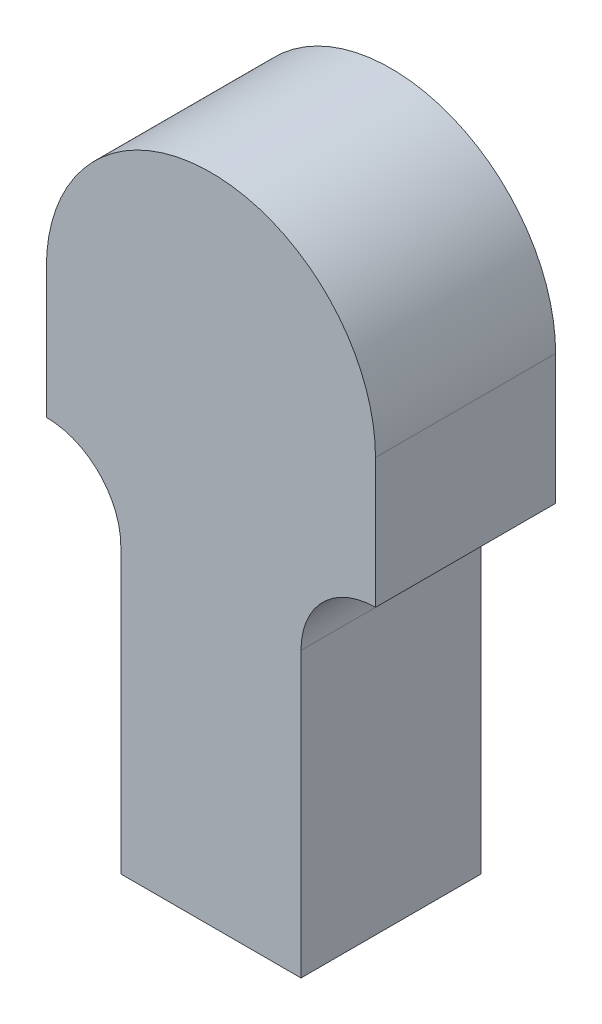
SolidWorks part; units mm, degrees
material "Stainless Steel (ferritic)"
ref_plane "Front Plane" through (0, 0, 0) normal (0, 0, 1) x (1, 0, 0)
ref_plane "Top Plane" through (0, 0, 0) normal (0, 1, 0) x (1, 0, 0)
ref_plane "Right Plane" through (0, 0, 0) normal (1, 0, 0) x (0, 0, -1)
sketch "Sketch1" plane through (0, 0, 0) normal (0, 0, 1) x (1, 0, 0)
  line L0 (-14.5, -18) -> (14.5, -18) construction
  line L1 (-7.9375, -18) -> (-7.9375, -43)
  line L2 (-14.5, 0) -> (-14.5, -11.4375)
  line L3 (-7.9375, -43) -> (7.9375, -43)
  line L4 (14.5, 0) -> (14.5, -11.4375)
  line L5 (7.9375, -18) -> (7.9375, -43)
  line L6 (0, -43) -> (0, 0) construction
  arc A0 (14.5, 0) -> (-14.5, 0) centre (0, 0) ccw
  arc A1 (-7.9375, -18) -> (-14.5, -11.4375) centre (-14.5, -18) ccw
  arc A2 (14.5, -11.4375) -> (7.9375, -18) centre (14.5, -18) ccw
  dimension "D1" = 29
  dimension "D2" = 18
  dimension "D4" = 15.875
  dimension "D3" = 43
extrude "Boss-Extrude1" add sketch "Sketch1" along normal blind 15.875
sketch "Sketch2" plane through (0, 0, 15.875) normal (0, 0, 1) x (1, 0, 0)
  circle A0 centre (0, 0) radius 5.9
  dimension "D1" = 11.8
extrude "Cut-Extrude1" [suppressed] cut sketch "Sketch2" against normal through all
sketch "Sketch3" plane through (0, 0, 15.875) normal (0, 0, 1) x (1, 0, 0)
  circle A0 centre (0, 0) radius 6.5
  dimension "D1" = 13
extrude "Cut-Extrude2" [suppressed] cut sketch "Sketch3" against normal offset from surface (13.875 mm away) 2
sketch "Sketch4" [suppressed] plane through (0, 0, 15.875) normal (0, 0, 1) x (1, 0, 0)
  circle A0 centre (0, 0) radius 14.5
  circle A1 centre (0, 0) radius 6.5 construction
  dimension "D1" = 8
extrude "Cut-Extrude3" [suppressed] cut sketch "Sketch4" against normal offset from surface (4.875 mm away) 9
fillet "Fillet1" [suppressed] radius 1
hole_wizard "M4x0.7 Tapped Hole1" [suppressed] positions "Sketch6" profile "Sketch5" tap size "M4x0.7" standard "Ansi Metric"
sketch "Sketch6" plane through (0, -43, 0) normal (0, -1, 0) x (1, 0, 0)
  line L0 (-7.9375, 15.875) -> (7.9375, 0) construction
  point P0 (0, 7.9375)
sketch "Sketch5" plane through (0, -43, 7.9375) normal (1, 0, 0) x (0, 0, -1)
  line L0 (0, 0) -> (0, 11.0914)
  line L1 (0, 11.0914) -> (1.65, 10.1)
  line L2 (1.65, 10.1) -> (1.65, 0)
  line L5 (1.65, 0) -> (0, 0)
  line L10 (0, 11.0914) -> (-1.65, 10.1) construction
  line L11 (0, -6.35) -> (0, 107.95) construction
  dimension "Tap Drill Dia." = 3.3
  dimension "Tap Drill Depth" = 10.1
  dimension "Drill Angle" = 118
cosmetic thread "Hole Thread1" [suppressed] parameters "D1"=8, "D2"=4
fillet "Fillet2" [suppressed] radius 4
